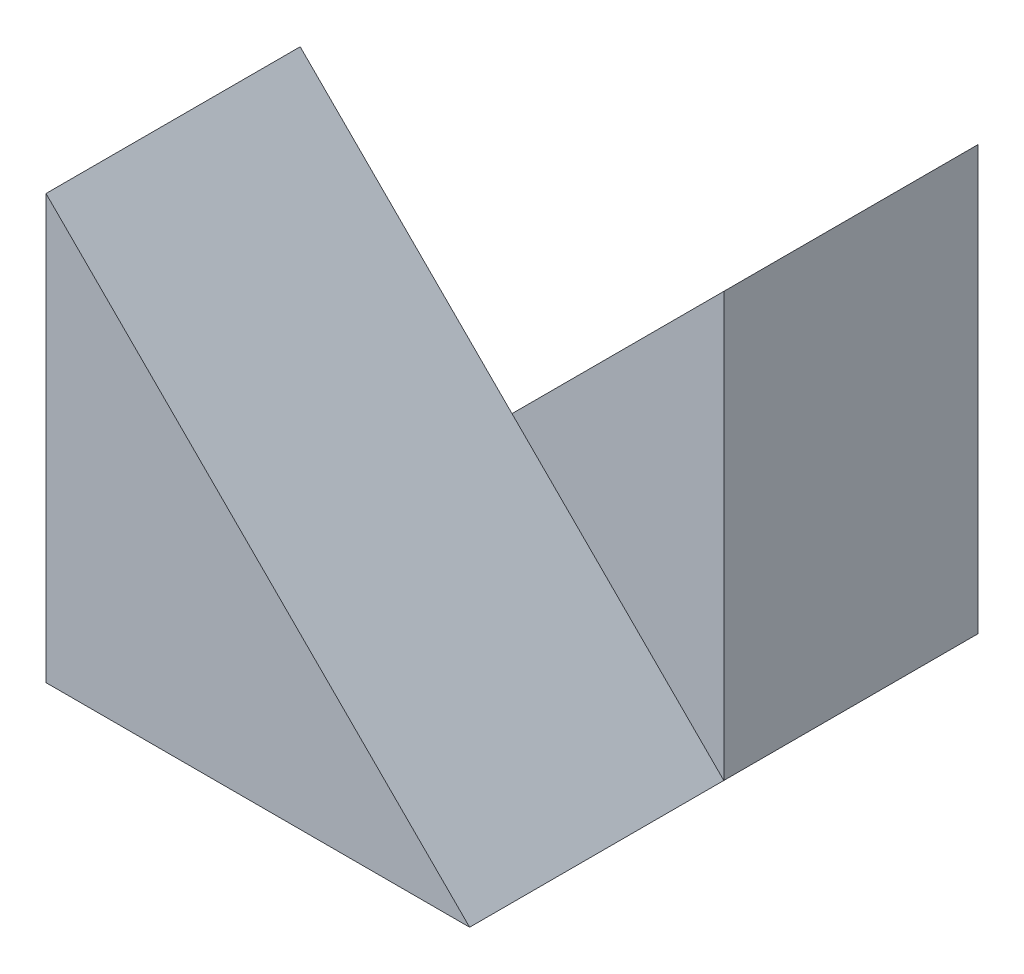
SolidWorks part; units mm, degrees
ref_plane "Front Plane" through (0, 0, 0) normal (0, 0, 1) x (1, 0, 0)
ref_plane "Top Plane" through (0, 0, 0) normal (0, 1, 0) x (1, 0, 0)
ref_plane "Right Plane" through (0, 0, 0) normal (1, 0, 0) x (0, 0, -1)
sketch "Sketch1" plane through (0, 0, 0) normal (0, 0, 1) x (1, 0, 0)
  line L0 (0, 25) -> (0, 0)
  line L1 (0, 0) -> (25, 0)
  line L2 (25, 0) -> (0, 25)
  dimension "D1" = 25
  dimension "D2" = 25
extrude "Boss-Extrude1" add sketch "Sketch1" along normal blind 15
sketch "Sketch2" plane through (0, 0, 0) normal (0, 0, -1) x (-1, 0, 0)
  line L0 (-25, 0) -> (-25, 25)
  line L1 (-25, 25) -> (0, 0)
  line L2 (0, 0) -> (-25, 0)
extrude "Boss-Extrude2" add sketch "Sketch2" along normal blind 15
